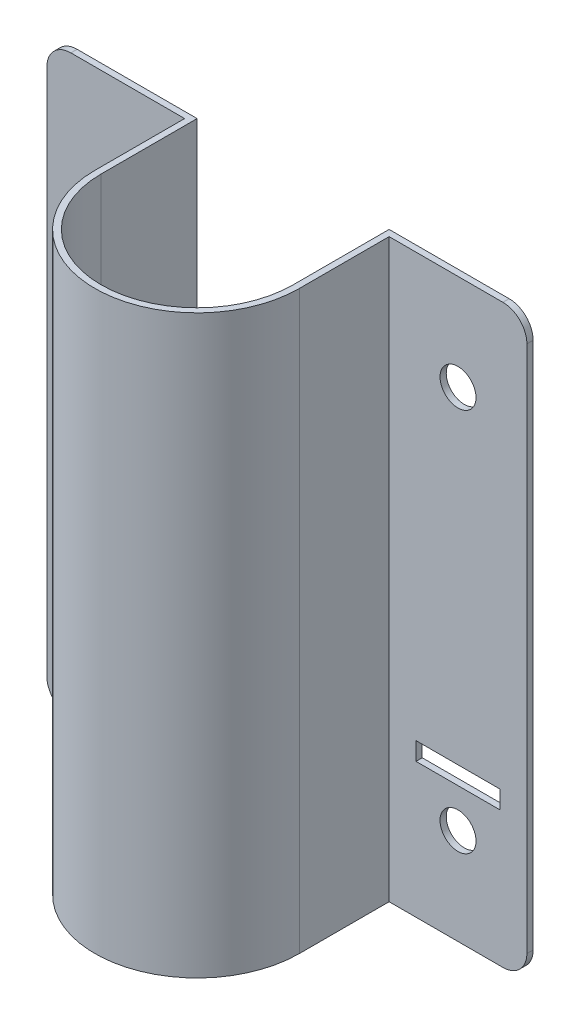
SolidWorks part; units mm, degrees
material "AISI 1020 Steel, Cold Rolled"
ref_plane "Front Plane" through (0, 0, 0) normal (0, 0, 1) x (1, 0, 0)
ref_plane "Top Plane" through (0, 0, 0) normal (0, 1, 0) x (1, 0, 0)
ref_plane "Right Plane" through (0, 0, 0) normal (1, 0, 0) x (0, 0, -1)
sketch "Sketch1" plane through (0, 0, 0) normal (0, 1, 0) x (1, 0, 0)
  line L0 (-27.051, 0) -> (-27.051, 23.749)
  line L1 (-27.051, 23.749) -> (-63.5, 23.749)
  line L2 (-25.4, 0) -> (-25.4, 25.4)
  line L3 (-25.4, 25.4) -> (-63.5, 25.4)
  line L4 (-63.5, 25.4) -> (-63.5, 23.749)
  line L5 (0, 0) -> (0, 38.1864) construction
  line L6 (25.4, 0) -> (25.4, 25.4)
  line L7 (27.051, 0) -> (27.051, 23.749)
  line L8 (63.5, 25.4) -> (63.5, 23.749)
  line L9 (25.4, 25.4) -> (63.5, 25.4)
  line L10 (27.051, 23.749) -> (63.5, 23.749)
  arc A0 (-25.4, 0) -> (25.4, 0) centre (0, 0) ccw
  arc A1 (-27.051, 0) -> (27.051, 0) centre (0, 0) ccw
  circle A3 centre (0, 0) radius 27.051 construction
  circle A4 centre (0, 0) radius 25.4 construction
  point P11 (27.051, 0)
  point P13 (24.2901, 7.4262)
  point P21 (0, -25.4)
  dimension "D1" = 50.8
  dimension "D3" = 1.651
  dimension "D4" = 38.1
  dimension "D5" = 50.8
  dimension "D2" = 1.651
extrude "Boss-Extrude1" add sketch "Sketch1" against normal blind 152.4
sketch "Sketch2" plane through (0, 0, -23.749) normal (0, 0, 1) x (1, 0, 0)
  line L0 (-45.2755, -152.4) -> (-45.2755, 0) construction
  line L1 (-63.5, -152.4) -> (-27.051, -152.4) construction
  line L2 (-63.5, 0) -> (-27.051, 0) construction
  line L3 (0, -152.4) -> (0, 0) construction
  line L4 (-27.051, -152.4) -> (27.051, -152.4) construction
  line L5 (27.051, 0) -> (-27.051, 0) construction
  line L6 (-63.5, 0) -> (-27.051, 0) construction
  line L7 (-63.5, -152.4) -> (-27.051, -152.4) construction
  circle A1 centre (-45.2755, -25.4) radius 4.7625
  circle A2 centre (45.2755, -25.4) radius 4.7625
  circle A4 centre (-45.2755, -127) radius 4.7625
  circle A5 centre (45.2755, -127) radius 4.7625
  dimension "D1" = 9.525
  dimension "D2" = 25.4
  dimension "D3" = 25.4
extrude "Cut-Extrude1" cut sketch "Sketch2" against normal blind 50.8
fillet "Fillet1" radius 6.35 4 edges at (63.5, 0, -24.5745) (63.5, -152.4, -24.5745) (-63.5, 0, -24.5745) (-63.5, -152.4, -24.5745)
sketch "Sketch3" plane through (0, 0, -23.749) normal (0, 0, 1) x (1, 0, 0)
  line L0 (45.2755, -25.4) -> (45.2755, -127) construction
  line L1 (0, 0) -> (0, -152.4) construction
  line L2 (56.388, -116.6812) -> (34.163, -116.6812)
  line L3 (56.388, -116.6812) -> (56.388, -111.9187)
  line L4 (56.388, -111.9187) -> (34.163, -111.9187)
  line L5 (34.163, -116.6812) -> (34.163, -111.9187)
  line L6 (56.388, -116.6812) -> (34.163, -111.9187) construction
  line L7 (56.388, -111.9187) -> (34.163, -116.6812) construction
  line L8 (-27.051, -152.4) -> (27.051, -152.4) construction
  line L9 (-56.388, -116.6813) -> (-34.163, -116.6813)
  line L10 (-56.388, -116.6813) -> (-56.388, -111.9188)
  line L11 (-56.388, -111.9188) -> (-34.163, -111.9188)
  line L12 (-34.163, -116.6813) -> (-34.163, -111.9188)
  point P4 (45.2755, -114.3)
  dimension "D1" = 4.7625
  dimension "D2" = 22.225
  dimension "D3" = 12.7
extrude "Cut-Extrude3" cut sketch "Sketch3" against normal through all
